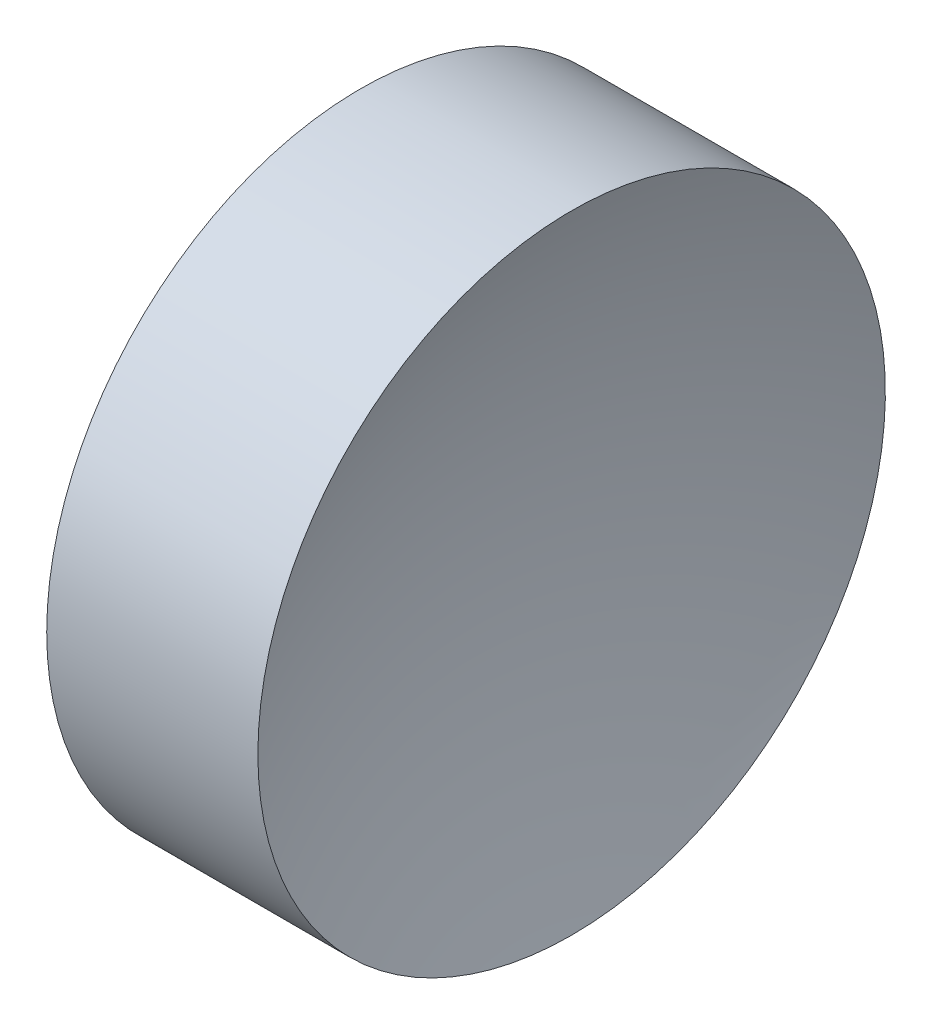
SolidWorks part; units mm, degrees
ref_plane "前视基准面" through (0, 0, 0) normal (0, 0, 1) x (1, 0, 0)
ref_plane "上视基准面" through (0, 0, 0) normal (0, 1, 0) x (1, 0, 0)
ref_plane "右视基准面" through (0, 0, 0) normal (1, 0, 0) x (0, 0, -1)
sketch "草图1" plane through (0, 0, 0) normal (0, 0, 1) x (1, 0, 0)
  line L0 (21.2249, 13.0445) -> (26.692, 13.0445) construction
  line L1 (22.1722, 13.0445) -> (22.1722, 16.1945)
  line L2 (23.6722, 13.0445) -> (22.1722, 13.0445)
  line L3 (22.1722, 16.1945) -> (24.2922, 16.1945)
  arc A0 (24.2922, 16.1945) -> (23.6722, 13.0445) centre (31.9842, 13.0445) ccw
revolve "旋转1" add sketch "草图1" angle 360 about L0
